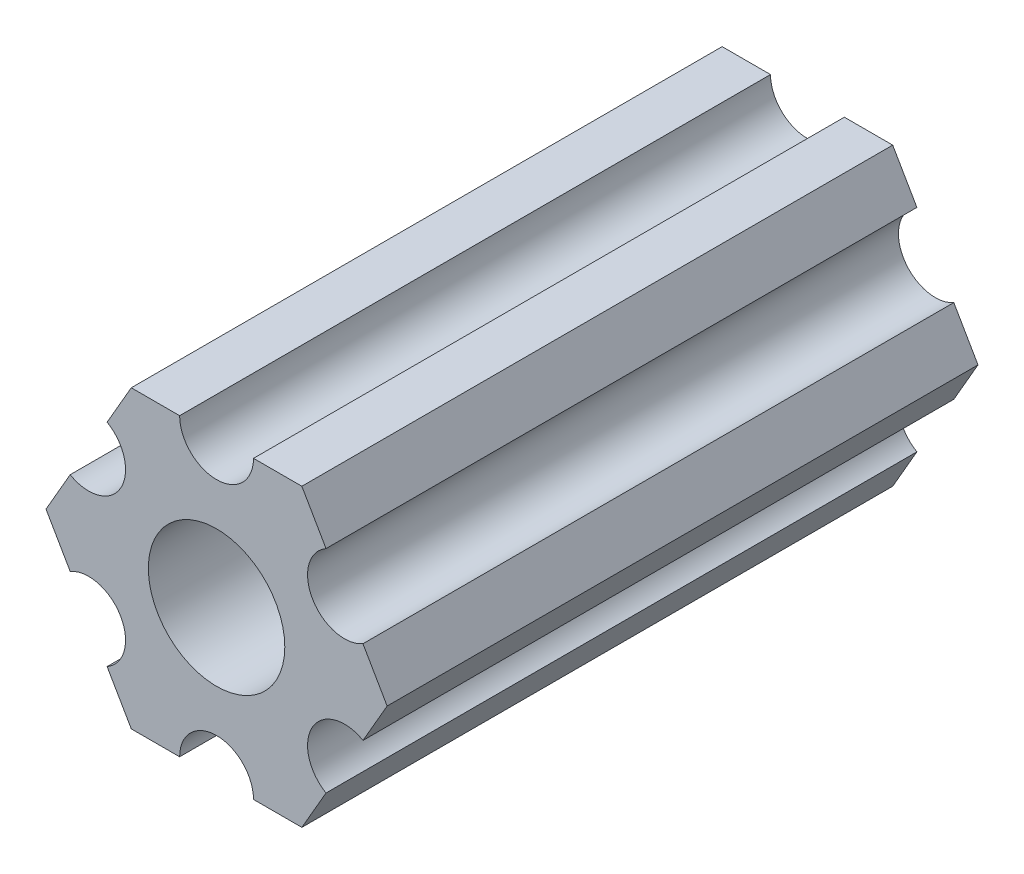
SolidWorks part; units mm, degrees
material "6061-T6 (SS)"
ref_plane "Front Plane" through (0, 0, 0) normal (0, 0, 1) x (1, 0, 0)
ref_plane "Top Plane" through (0, 0, 0) normal (0, 1, 0) x (1, 0, 0)
ref_plane "Right Plane" through (0, 0, 0) normal (1, 0, 0) x (0, 0, -1)
ref_plane "Plane1" through (0, 0, 0) normal (0, 0, -1) x (-1, 0, 0)
sketch "Sketch1" plane through (0, 0, 0) normal (0, 0, -1) x (-1, 0, 0)
  line L0 (-4.7055, -4.5498) -> (-3.6662, -6.35)
  line L1 (-3.6662, -6.35) -> (-1.5875, -6.35)
  line L2 (1.5875, -6.35) -> (3.6662, -6.35)
  line L3 (3.6662, -6.35) -> (4.7055, -4.5498)
  line L4 (6.293, -1.8002) -> (7.3323, 0)
  line L5 (7.3323, 0) -> (6.293, 1.8002)
  line L6 (4.7055, 4.5498) -> (3.6662, 6.35)
  line L7 (3.6662, 6.35) -> (1.5875, 6.35)
  line L8 (-1.5875, 6.35) -> (-3.6662, 6.35)
  line L9 (-3.6662, 6.35) -> (-4.7055, 4.5498)
  line L10 (-6.293, 1.8002) -> (-7.3323, 0)
  line L11 (-7.3323, 0) -> (-6.293, -1.8002)
  circle A0 centre (0, 0) radius 2.9337
  arc A1 (-6.293, -1.8002) -> (-4.7055, -4.5498) centre (-5.4993, -3.175) cw
  arc A2 (-1.5875, -6.35) -> (1.5875, -6.35) centre (0, -6.35) cw
  arc A3 (4.7055, -4.5498) -> (6.293, -1.8002) centre (5.4993, -3.175) cw
  arc A4 (6.293, 1.8002) -> (4.7055, 4.5498) centre (5.4993, 3.175) cw
  arc A5 (1.5875, 6.35) -> (-1.5875, 6.35) centre (0, 6.35) cw
  arc A6 (-4.7055, 4.5498) -> (-6.293, 1.8002) centre (-5.4993, 3.175) cw
extrude "Boss-Extrude1" add sketch "Sketch1" against normal mid plane 25.4
